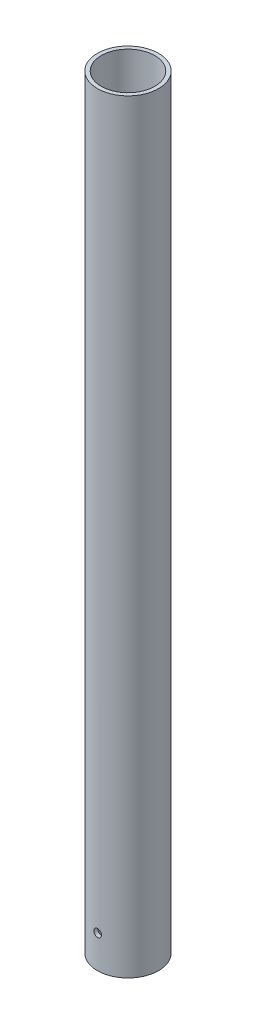
SolidWorks part; units mm, degrees
ref_plane "Front Plane" through (0, 0, 0) normal (0, 0, 1) x (1, 0, 0)
ref_plane "Top Plane" through (0, 0, 0) normal (0, 1, 0) x (1, 0, 0)
ref_plane "Right Plane" through (0, 0, 0) normal (1, 0, 0) x (0, 0, -1)
sketch "Sketch1" plane through (0, 0, 0) normal (0, 1, 0) x (1, 0, 0)
  circle A0 centre (0, 0) radius 8
  circle A1 centre (0, 0) radius 7
extrude "Boss-Extrude1" add sketch "Sketch1" along normal blind 200
sketch "Sketch2" plane through (0, 0, 0) normal (0, 0, 1) x (1, 0, 0)
  circle A0 centre (0, 8.5636) radius 1
extrude "Cut-Extrude1" cut sketch "Sketch2" against normal through all and the other way through all
